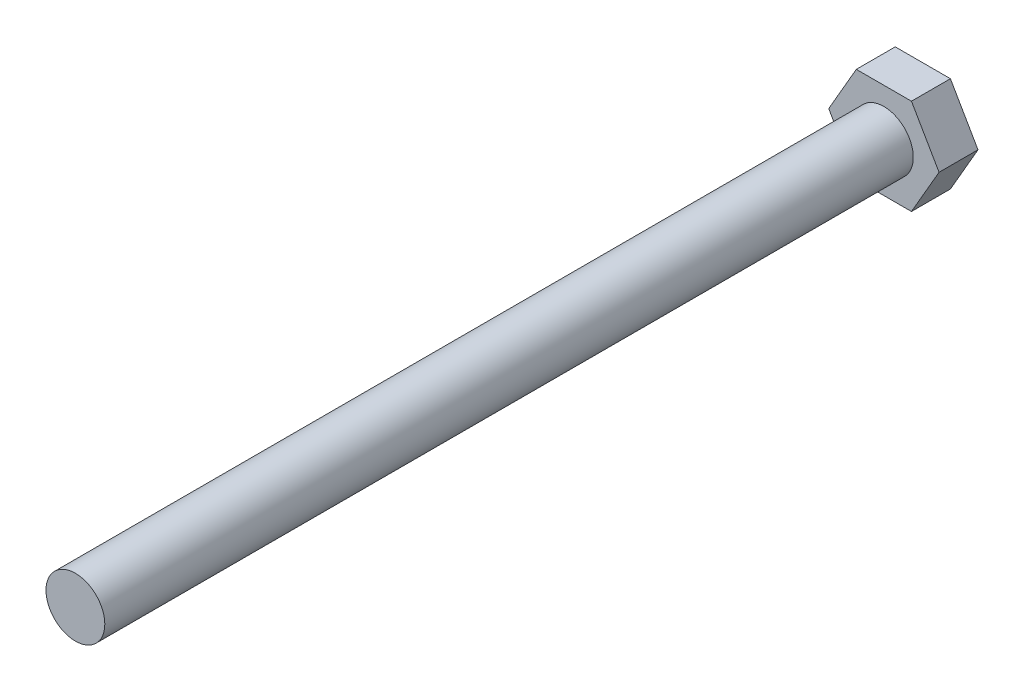
SolidWorks part; units mm, degrees
ref_plane "Plane1" through (0, 0, 0) normal (0, 0, 1) x (1, 0, 0)
ref_plane "Plane2" through (0, 0, 0) normal (0, 1, 0) x (1, 0, 0)
ref_plane "Plane3" through (0, 0, 0) normal (1, 0, 0) x (0, 0, -1)
sketch "Sketch1" plane through (0, 0, 0) normal (0, 0, 1) x (1, 0, 0)
  line L0 (7.5056, 0) -> (3.7528, 6.5)
  line L1 (3.7528, 6.5) -> (-3.7528, 6.5)
  line L2 (-3.7528, 6.5) -> (-7.5056, 0)
  line L3 (-7.5056, 0) -> (-3.7528, -6.5)
  line L4 (-3.7528, -6.5) -> (3.7528, -6.5)
  line L5 (3.7528, -6.5) -> (7.5056, 0)
  circle A0 centre (0, 0) radius 6.5 construction
  dimension "Nøglevidde" = 13
extrude "Base-Extrude" add sketch "Sketch1" along normal blind 5.3
sketch "Sketch2" plane through (0, 0, 5.3) normal (0, 0, 1) x (1, 0, 0)
  circle A0 centre (0, 0) radius 4
  dimension "Gevind" = 8
extrude "Boss-Extrude1" add sketch "Sketch2" along normal blind 110
